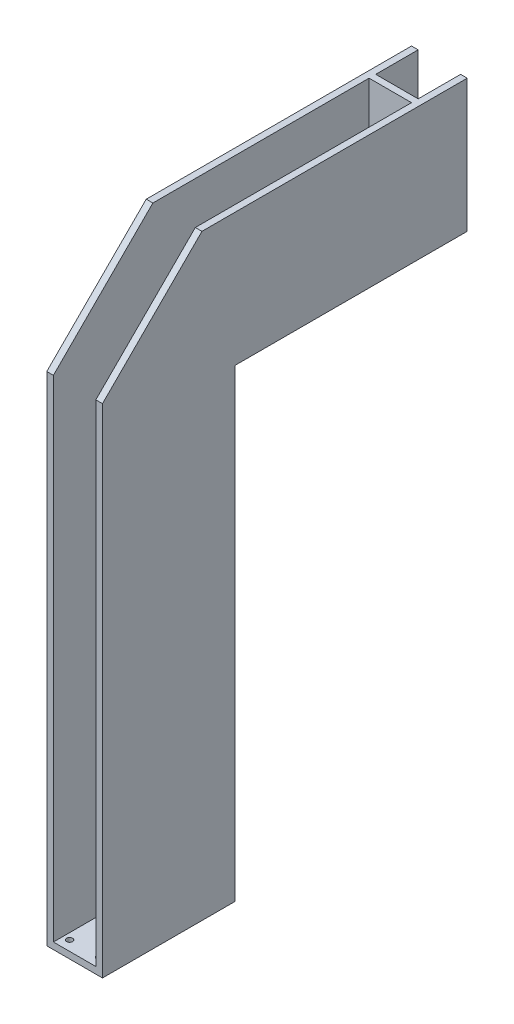
SolidWorks part; units mm, degrees
ref_plane "Front Plane" through (0, 0, 0) normal (0, 0, 1) x (1, 0, 0)
ref_plane "Top Plane" through (0, 0, 0) normal (0, 1, 0) x (1, 0, 0)
ref_plane "Right Plane" through (0, 0, 0) normal (1, 0, 0) x (0, 0, -1)
sketch "Sketch1" plane through (0, 0, 0) normal (1, 0, 0) x (0, 0, -1)
  line L0 (0, 0) -> (0, 750)
  line L1 (0, 750) -> (150, 900)
  line L2 (150, 900) -> (550, 900)
  line L3 (550, 900) -> (550, 700)
  line L4 (550, 700) -> (200, 700)
  line L5 (200, 700) -> (200, 0)
  line L6 (200, 0) -> (0, 0)
  dimension "D1" = 200
  dimension "D2" = 900
  dimension "D3" = 750
  dimension "D4" = 200
  dimension "D5" = 550
  dimension "D6" = 45
extrude "Boss-Extrude1" add sketch "Sketch1" along normal blind 10 and the other way blind 74
sketch "Sketch3" plane through (0, 900, 0) normal (0, 1, 0) x (1, 0, 0)
  line L0 (-74, 550) -> (10, 550) construction
  line L1 (-64, 550) -> (0, 550)
  line L2 (-64, 550) -> (-64, 0)
  line L3 (-64, 0) -> (0, 0)
  line L4 (0, 550) -> (0, 0)
  line L5 (-74, 0) -> (10, 0) construction
  point P8 (-32, 550)
  point P9 (-32, 550)
  dimension "D1" = 64
extrude "Cut-Extrude1" cut sketch "Sketch3" against normal offset from surface (890 mm away) 10 up to face at (-32, 0, -100)
sketch "Sketch4" plane through (0, 700, 0) normal (0, -1, 0) x (1, 0, 0)
  line L1 (-64, -550) -> (0, -550)
  line L2 (-64, -550) -> (-64, -200)
  line L3 (-64, -200) -> (0, -200)
  line L4 (0, -550) -> (0, -200)
extrude "Boss-Extrude2" add sketch "Sketch4" against normal blind 10
ref_plane "Plane1" through (0, 0, -486) normal (0, 0, -1) x (-1, 0, 0)
sketch "Sketch5" plane through (0, 0, -486) normal (0, 0, -1) x (-1, 0, 0)
  line L1 (0, 710) -> (64, 710)
  line L2 (0, 710) -> (0, 900)
  line L3 (0, 900) -> (64, 900)
  line L4 (64, 710) -> (64, 900)
extrude "Boss-Extrude3" add sketch "Sketch5" against normal blind 10
sketch "Sketch6" plane through (0, 710, 0) normal (0, 1, 0) x (1, 0, 0)
  line L2 (0, 486) -> (0, 550) construction
  line L4 (-64, 486) -> (0, 486) construction
  circle A4 centre (-8.5, 494.5) radius 4.5
  circle A5 centre (-55, 494.5) radius 4.5
  circle A6 centre (-55, 541) radius 4.5
  circle A7 centre (-8.5, 541) radius 4.5
  dimension "D1" = 9
  dimension "D2" = 8.5
  dimension "D3" = 8.5
  dimension "D4" = 46.5
  dimension "D5" = 46.5
extrude "Cut-Extrude2" cut sketch "Sketch6" against normal up to next
sketch "Sketch7" plane through (0, 0, -476) normal (0, 0, 1) x (1, 0, 0)
  line L0 (0, 710) -> (-64, 710) construction
  line L1 (0, 900) -> (0, 710) construction
  circle A0 centre (-26.25, 732.5) radius 8
  dimension "D1" = 16
  dimension "D2" = 22.5
  dimension "D3" = 26.25
extrude "Cut-Extrude3" cut sketch "Sketch7" against normal up to next
sketch "Sketch8" plane through (0, 10, 0) normal (0, 1, 0) x (1, 0, 0)
  line L0 (-54.5, 15) -> (-9.5, 15) construction
  line L1 (-9.5, 15) -> (-9.5, 185) construction
  line L2 (-9.5, 185) -> (-54.5, 185) construction
  line L3 (-54.5, 185) -> (-54.5, 15) construction
  line L4 (0, 200) -> (-64, 200) construction
  line L5 (0, 0) -> (0, 200) construction
  circle A0 centre (-54.5, 185) radius 4.5
  circle A1 centre (-54.5, 165) radius 5
  circle A2 centre (-54.5, 15) radius 4.5
  circle A3 centre (-9.5, 15) radius 4.5
  circle A4 centre (-9.5, 35) radius 5
  circle A5 centre (-9.5, 185) radius 4.5
  point P14 (-32, 200)
  point P15 (-32, 185)
  point P18 (0, 100)
  point P19 (-9.5, 100)
  dimension "D1" = 45
  dimension "D3" = 9
  dimension "D4" = 10
  dimension "D6" = 20
  dimension "D2" = 170
  dimension "D5" = 20
extrude "Cut-Extrude4" cut sketch "Sketch8" against normal up to next
